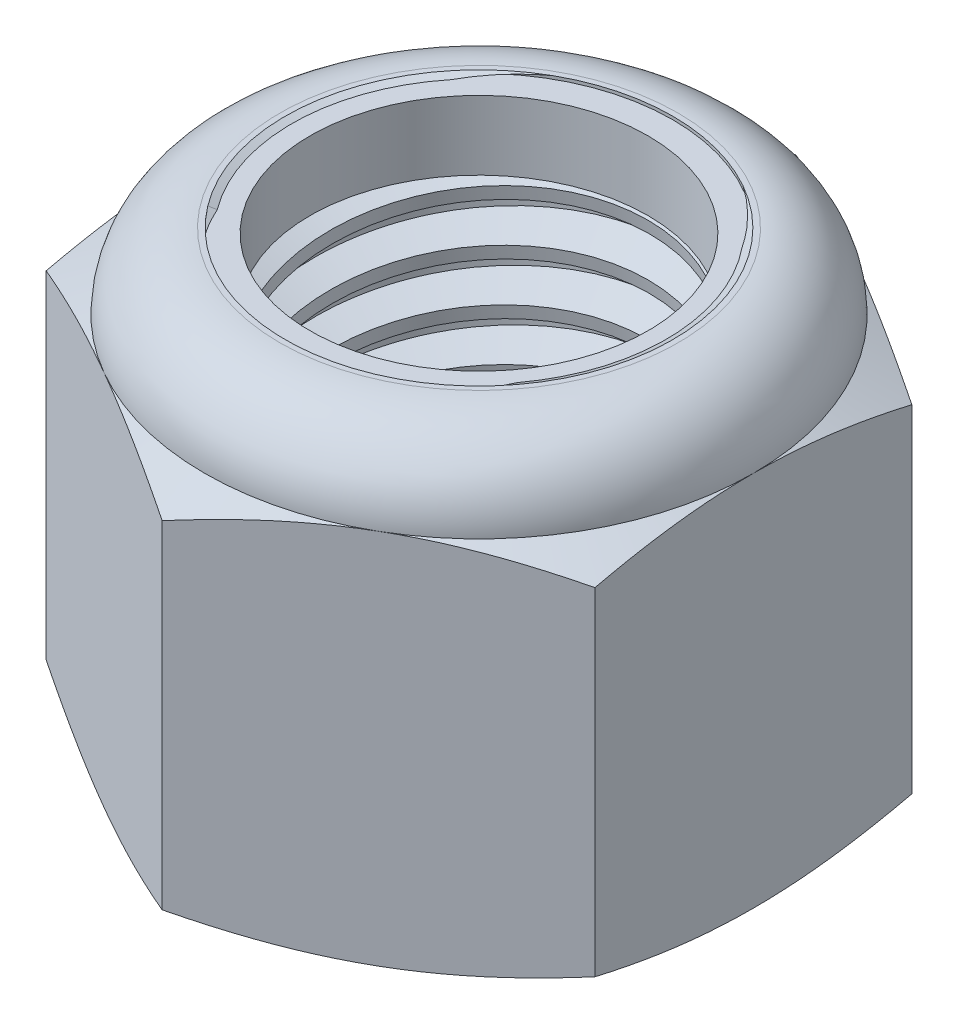
SolidWorks part; units mm, degrees
material "Plain Carbon Steel"
ref_plane "Front" through (0, 0, 0) normal (0, 0, 1) x (1, 0, 0)
ref_plane "Top" through (0, 0, 0) normal (0, 1, 0) x (1, 0, 0)
ref_plane "Right" through (0, 0, 0) normal (1, 0, 0) x (0, 0, -1)
sketch "Sketch1" plane through (0, 0, 0) normal (0, 1, 0) x (1, 0, 0)
  line L1 (0, 15.5812) -> (-13.4938, 7.7906)
  line L2 (-13.4938, 7.7906) -> (-13.4937, -7.7906)
  line L3 (-13.4937, -7.7906) -> (0, -15.5812)
  line L4 (0, -15.5812) -> (13.4937, -7.7906)
  line L5 (13.4937, -7.7906) -> (13.4937, 7.7906)
  line L6 (13.4937, 7.7906) -> (0, 15.5812)
  circle A0 centre (0, 0) radius 13.4938 construction
  dimension "Hex Flats" = 26.9875
extrude "Extrude1" add sketch "Sketch1" along normal blind 22.225
sketch "Sketch2" plane through (0, 0, 0) normal (1, 0, 0) x (0, 0, -1)
  line L0 (-9.525, 0) -> (-9.525, 22.225) construction
  line L1 (0, 0) -> (9.525, 0)
  line L2 (0, 0) -> (0, 22.225)
  line L3 (0, 22.225) -> (9.525, 22.225)
  line L4 (9.525, 0) -> (9.525, 22.225)
  line L5 (-7.7906, 22.225) -> (7.7906, 22.225) construction
  line L7 (0, -9.525) -> (0, 0) construction
  dimension "Thread Dia" = 19.05
revolve "Revolve1" add sketch "Sketch2" angle 360 about L7
sketch "Sketch3" plane through (0, 0, 0) normal (1, 0, 0) x (0, 0, -1)
  line L0 (9.525, 22.225) -> (-9.525, 22.225) construction
  line L1 (-9.525, 22.225) -> (-9.525, 19.685) construction
  line L2 (-9.525, 19.685) -> (9.525, 22.225) construction
  line L3 (9.525, 22.225) -> (9.567, 21.9103) construction
  line L4 (9.567, 21.9103) -> (9.8607, 19.7073)
  line L5 (9.8607, 19.7073) -> (8.393, 20.3124)
  line L6 (8.393, 20.3124) -> (8.3091, 20.9418)
  line L7 (8.3091, 20.9418) -> (9.567, 21.9103)
  line L8 (8.3511, 20.6271) -> (9.7138, 20.8088) construction
  line L9 (9.525, 22.225) -> (9.525, 20.7836) construction
  line L10 (9.525, 20.7836) -> (-9.525, 18.2436) construction
  line L11 (-9.525, 18.2436) -> (-9.525, 19.685) construction
  line L12 (-0.3615, 22.225) -> (0.3615, 16.8022) construction
  line L13 (-9.525, 0) -> (-9.525, 22.225) construction
  line L14 (0, 22.225) -> (9.525, 22.225) construction
  line L15 (9.525, 0) -> (9.525, 22.225) construction
  point P13 (0, 19.5136)
  dimension "D1" = 0.3175
  dimension "D2" = 0.635
  dimension "Thread Pitch" = 2.54
  dimension "D4" = 60
  dimension "D5" = 2.54
revolve "Cut-Revolve1" cut sketch "Sketch3" angle 360 about L12
pattern_linear "LPattern1" count 9 spacing 2.54 along (0, -1, 0) count 2 spacing 2.54 along (0, 1, 0) of "Cut-Revolve1"
sketch "Sketch4" plane through (0, 0, 0) normal (1, 0, 0) x (0, 0, -1)
  line L0 (0, 22.225) -> (9.525, 22.225)
  line L1 (9.525, 22.225) -> (8.3091, 21.658)
  line L2 (8.3091, 21.658) -> (8.3091, 0.567)
  line L3 (8.3091, 0.567) -> (9.525, 0)
  line L4 (9.525, 0) -> (0, 0)
  line L5 (0, 0) -> (0, 22.225)
  line L6 (9.525, 0) -> (9.525, 22.225) construction
  line L7 (0, 22.225) -> (9.525, 22.225) construction
  line L8 (0, 0) -> (9.525, 0) construction
  line L9 (0, 0) -> (0, 22.225) construction
  line L10 (0, 22.225) -> (0, 23.5666) construction
  dimension "D1" = 25
revolve "Cut-Revolve2" cut sketch "Sketch4" angle 360 about L10
combine bodies "Combine1" operation type subtract main body 112 bodies to subtract 111
sketch "Sketch5" plane through (0, 0, 0) normal (1, 0, 0) x (0, 0, -1)
  line L0 (0, 0) -> (13.4938, 0)
  line L1 (13.4938, 0) -> (15.5812, 0.9734)
  line L2 (15.5812, 0.9734) -> (15.5812, 17.5474)
  line L3 (15.5812, 17.5474) -> (13.4937, 18.5208)
  line L4 (9.7896, 22.225) -> (9.7896, 23.495)
  line L5 (9.7896, 23.495) -> (16.8512, 23.495)
  line L6 (16.8512, 23.495) -> (16.8512, -1.27)
  line L7 (16.8512, -1.27) -> (0, -1.27)
  line L8 (0, -1.27) -> (0, 0)
  line L9 (13.4937, 18.5208) -> (13.4938, 0) construction
  line L10 (0, 0) -> (9.525, 0) construction
  line L13 (15.5812, 9.2604) -> (16.8512, 9.2604) construction
  line L14 (15.5812, 22.225) -> (15.5812, 0) construction
  line L15 (0, 0) -> (0, 23.495) construction
  line L20 (0, 23.495) -> (9.7896, 23.495) construction
  line L22 (0, 22.225) -> (9.525, 22.225) construction
  arc A0 (13.4937, 18.5208) -> (9.7896, 22.225) centre (9.7896, 18.5208) ccw
  dimension "D1" = 25
  dimension "D2" = 1.27
  dimension "D3" = 22.225
  dimension "D4" = 3.7042
revolve "Cut-Revolve3" cut sketch "Sketch5" angle 360 about L15
sketch "Sketch6" plane through (0, 0, 0) normal (1, 0, 0) x (0, 0, -1)
  line L0 (0, 18.5208) -> (13.3413, 18.5208)
  line L1 (9.7896, 22.0726) -> (9.0493, 22.0726)
  line L2 (0, 23.495) -> (0, 18.5208)
  line L3 (9.0493, 23.495) -> (0, 23.495)
  line L4 (0, 23.495) -> (9.7896, 23.495) construction
  line L5 (0, 0) -> (0, 23.495) construction
  line L6 (0, 23.495) -> (0, 44.323) construction
  line L7 (9.0493, 22.0726) -> (9.0493, 23.495)
  line L8 (9.7896, 22.225) -> (9.7896, 22.0726) construction
  line L9 (9.0493, 22.0726) -> (8.3091, 22.0726) construction
  line L10 (8.3091, 22.0726) -> (8.3091, 21.658) construction
  arc A0 (13.3413, 18.5208) -> (9.7896, 22.0726) centre (9.7896, 18.5208) ccw
  arc A1 (13.4937, 18.5208) -> (9.7896, 22.225) centre (9.7896, 18.5208) ccw construction
  dimension "D1" = 0.1524
revolve "Cut-Revolve4" cut sketch "Sketch6" angle 360 about L6
sketch "Sketch7" plane through (0, 0, 0) normal (1, 0, 0) x (0, 0, -1)
  line L0 (8.3091, 18.597) -> (13.2643, 18.597)
  line L1 (9.7896, 21.9964) -> (8.3091, 21.9964)
  line L2 (8.3091, 21.9964) -> (8.3091, 18.597)
  line L3 (8.3091, 18.597) -> (0, 18.597) construction
  line L4 (0, 18.597) -> (0, 21.9964) construction
  line L5 (0, 21.9964) -> (8.3091, 21.9964) construction
  line L6 (8.3091, 18.597) -> (8.3091, 18.5208) construction
  line L7 (0, 18.5208) -> (13.3413, 18.5208) construction
  line L8 (9.7896, 21.9964) -> (9.7896, 22.0726) construction
  arc A0 (13.2643, 18.597) -> (9.7896, 21.9964) centre (9.7896, 18.5208) ccw
  arc A2 (13.3413, 18.5208) -> (9.7896, 22.0726) centre (9.7896, 18.5208) ccw construction
  dimension "D1" = 0.0762
revolve "Revolve2" add sketch "Sketch7" angle 360 about L4
equation "\"D1@Sketch3\"=\"Thread Pitch@Sketch3\"/8"
equation "\"D2@Sketch3\"=\"Thread Pitch@Sketch3\"/4"
equation "\"D5@Sketch3\"=\"Thread Pitch@Sketch3\""
equation "\"D4@LPattern1\"=\"Thread Pitch@Sketch3\""
equation "\"D3@LPattern1\"=\"Thread Pitch@Sketch3\""
equation "\"D1@LPattern1\"=\"Height@Extrude1\"/\"Thread Pitch@Sketch3\""
equation "\"D4@Sketch5\"=\"Height@Extrude1\"/6"
